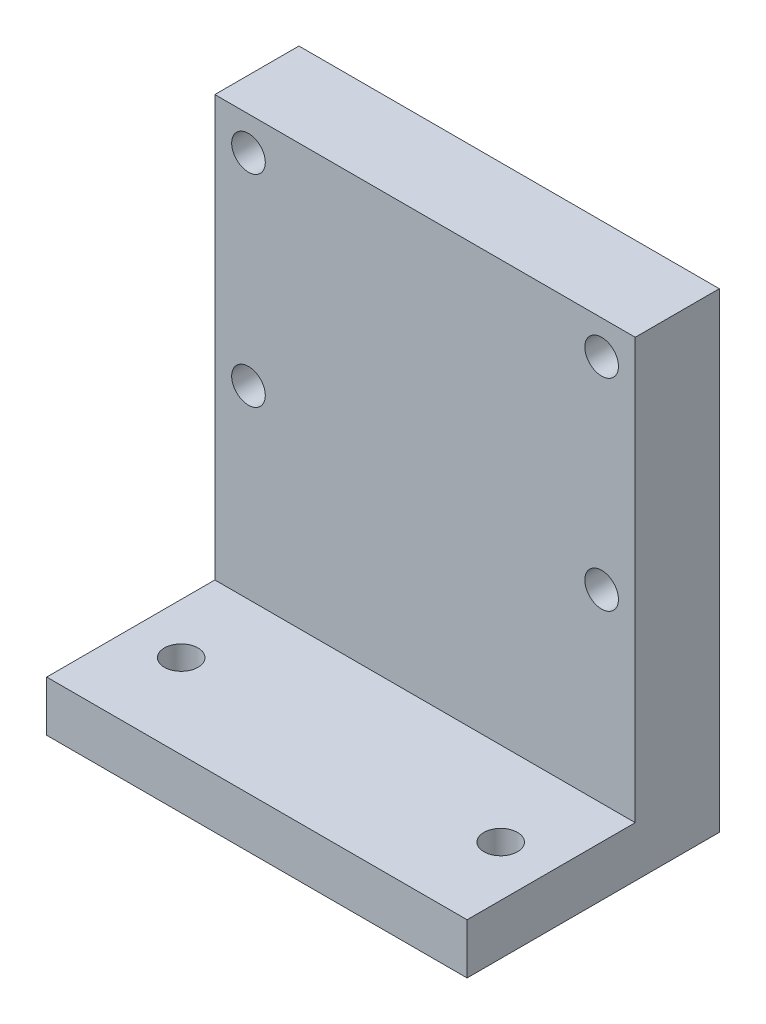
SolidWorks part; units mm, degrees
ref_plane "Front Plane" through (0, 0, 0) normal (0, 0, 1) x (1, 0, 0)
ref_plane "Top Plane" through (0, 0, 0) normal (0, 1, 0) x (1, 0, 0)
ref_plane "Right Plane" through (0, 0, 0) normal (1, 0, 0) x (0, 0, -1)
sketch "Sketch2" plane through (0, 0, 0) normal (0, 0, 1) x (1, 0, 0)
  line L1 (7.1229, 17.5978) -> (-17.8771, 17.5978)
  line L2 (7.1229, 17.5978) -> (7.1229, -17.4022)
  line L3 (7.1229, -17.4022) -> (-17.8771, -17.4022)
  line L4 (-17.8771, 17.5978) -> (-17.8771, -17.4022)
  dimension "D1" = 35
  dimension "D2" = 25
extrude "Boss-Extrude2" add sketch "Sketch2" along normal blind 35
sketch "Sketch3" plane through (0, 0, 35) normal (0, 0, 1) x (1, 0, 0)
  line L0 (7.1229, -17.4022) -> (7.1229, 17.5978) construction
  line L1 (-17.8771, 17.5978) -> (7.1229, 17.5978)
  line L2 (-17.8771, 17.5978) -> (-17.8771, -7.4022)
  line L3 (-17.8771, -7.4022) -> (7.1229, -7.4022)
  line L4 (7.1229, 17.5978) -> (7.1229, -7.4022)
  dimension "D1" = 25
extrude "Cut-Extrude1" cut sketch "Sketch3" against normal blind 25
sketch "Sketch5" plane through (0, 0, 35) normal (0, 0, 1) x (1, 0, 0)
  line L1 (-17.8771, -7.4022) -> (7.1229, -7.4022)
  line L2 (-17.8771, -7.4022) -> (-17.8771, -17.4022)
  line L3 (-17.8771, -17.4022) -> (7.1229, -17.4022)
  line L4 (7.1229, -7.4022) -> (7.1229, -17.4022)
extrude "Cut-Extrude2" cut sketch "Sketch5" against normal blind 15
sketch "Sketch6" plane through (0, -7.4022, 0) normal (0, 1, 0) x (1, 0, 0)
  circle A0 centre (-14.8779, -15) radius 1
  circle A1 centre (4.1229, -15) radius 1
extrude "Cut-Extrude3" cut sketch "Sketch6" against normal blind 15
sketch "Sketch7" plane through (0, -17.4022, 0) normal (0, -1, 0) x (1, 0, 0)
  line L1 (-17.8771, 20) -> (7.1229, 20)
  line L2 (-17.8771, 20) -> (-17.8771, 0)
  line L3 (-17.8771, 0) -> (7.1229, 0)
  line L4 (7.1229, 20) -> (7.1229, 0)
extrude "Cut-Extrude4" cut sketch "Sketch7" against normal blind 7
sketch "Sketch9" plane through (0, 0, 10) normal (0, 0, 1) x (1, 0, 0)
  circle A0 centre (-15.8771, 15.5978) radius 1
  circle A1 centre (5.1229, 15.5978) radius 1
  circle A3 centre (-15.8771, 3.5978) radius 1
  circle A4 centre (5.1229, 3.5978) radius 1
extrude "Cut-Extrude6" cut sketch "Sketch9" against normal blind 15
sketch "Sketch10" plane through (0, 0, 0) normal (0, 0, -1) x (-1, 0, 0)
  line L1 (-7.1229, -10.4022) -> (17.8771, -10.4022)
  line L2 (-7.1229, -10.4022) -> (-7.1229, 17.5978)
  line L3 (-7.1229, 17.5978) -> (17.8771, 17.5978)
  line L4 (17.8771, -10.4022) -> (17.8771, 17.5978)
extrude "Cut-Extrude7" cut sketch "Sketch10" against normal blind 5
